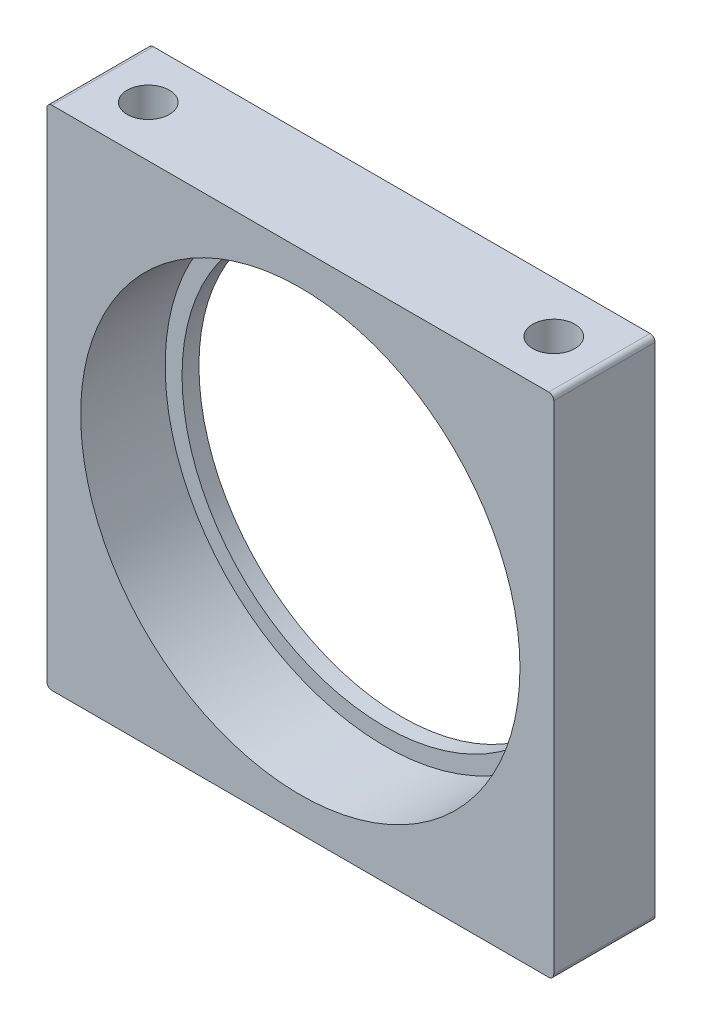
SolidWorks part; units mm, degrees
ref_plane "Plan de face" through (0, 0, 0) normal (0, 0, 1) x (1, 0, 0)
ref_plane "Plan de dessus" through (0, 0, 0) normal (0, 1, 0) x (1, 0, 0)
ref_plane "Plan de droite" through (0, 0, 0) normal (1, 0, 0) x (0, 0, -1)
sketch "Esquisse1" plane through (0, 0, 0) normal (0, 0, 1) x (1, 0, 0)
  line L1 (0, 0) -> (30, 0)
  line L2 (0, 0) -> (0, 30)
  line L3 (0, 30) -> (30, 30)
  line L4 (30, 0) -> (30, 30)
  circle A0 centre (15, 15) radius 12
  point P9 (10.0095, 0)
  dimension "D3" = 24
  dimension "D1" = 30
  dimension "D2" = 30
  dimension "D4" = 15
  dimension "D5" = 15
extrude "Boss.-Extru.1" add sketch "Esquisse1" along normal blind 6
sketch "Esquisse2" plane through (0, 0, 6) normal (0, 0, 1) x (1, 0, 0)
  line L0 (30, 30) -> (0, 30) construction
  line L1 (0, 30) -> (0, 0) construction
  circle A0 centre (15, 15) radius 13
  dimension "D3" = 26
  dimension "D1" = 15
  dimension "D2" = 15
extrude "Enlèv. mat.-Extru.1" cut sketch "Esquisse2" against normal blind 5
hole_wizard "Trou pour taraudage pour trou taraudé M31" positions "Esquisse3" profile "Esquisse4" hole size "M3" standard "ISO"
sketch "Esquisse3" plane through (0, 30, 0) normal (0, 1, 0) x (1, 0, 0)
  line L0 (30, 0) -> (0, 0) construction
  line L1 (0, -6) -> (0, 0) construction
  line L2 (30, -6) -> (30, 0) construction
  point P0 (3, -3)
  point P2 (27, -3)
  dimension "D1" = 3
  dimension "D2" = 3
  dimension "D3" = 3
  dimension "D4" = 3
sketch "Esquisse4" plane through (3, 30, 3) normal (1, 0, 0) x (0, 0, 1)
  line L0 (0, 0) -> (0, 6.7511)
  line L1 (0, 6.7511) -> (1.25, 6)
  line L2 (1.25, 6) -> (1.25, 0)
  line L5 (1.25, 0) -> (0, 0)
  line L10 (0, 6.7511) -> (-1.25, 6) construction
  line L11 (0, -6.35) -> (0, 107.95) construction
  dimension "Diamètre du perçage" = 2.5
  dimension "Profondeur du perçage" = 6
  dimension "Angle de pointe" = 118
hole_wizard "Trou pour taraudage pour trou taraudé M32" positions "Esquisse5" profile "Esquisse6" hole size "M3" standard "ISO"
sketch "Esquisse5" plane through (0, 0, 0) normal (0, -1, 0) x (-1, 0, 0)
  line L0 (-30, -6) -> (-30, 0) construction
  line L1 (0, -6) -> (0, 0) construction
  line L2 (0, 0) -> (-30, 0) construction
  point P0 (-3, -3)
  point P2 (-27, -3)
  dimension "D1" = 3
  dimension "D2" = 3
  dimension "D3" = 3
  dimension "D4" = 3
sketch "Esquisse6" plane through (3, 0, 3) normal (1, 0, 0) x (0, 0, -1)
  line L0 (0, 0) -> (0, 6.7511)
  line L1 (0, 6.7511) -> (1.25, 6)
  line L2 (1.25, 6) -> (1.25, 0)
  line L5 (1.25, 0) -> (0, 0)
  line L10 (0, 6.7511) -> (-1.25, 6) construction
  line L11 (0, -6.35) -> (0, 107.95) construction
  dimension "Diamètre du perçage" = 2.5
  dimension "Profondeur du perçage" = 6
  dimension "Angle de pointe" = 118
fillet "Congé1" radius 0.3 4 edges at (30, 0, 3) (0, 0, 3) (0, 30, 3) (30, 30, 3)
